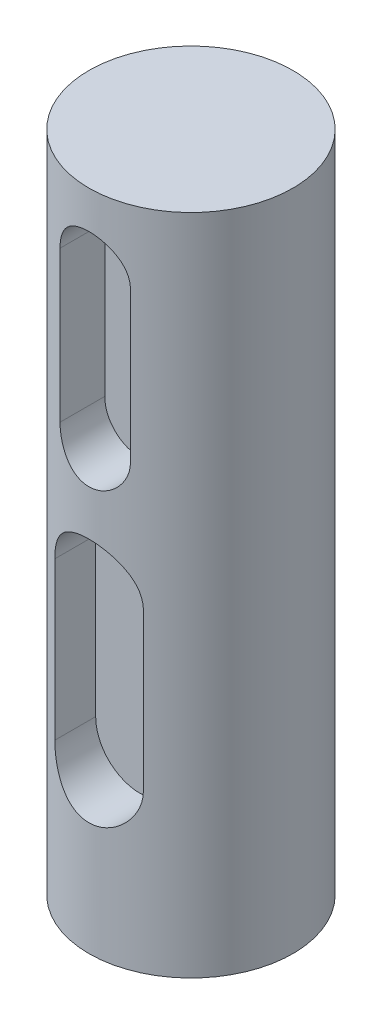
SolidWorks part; units mm, degrees
ref_plane "前视基准面" through (0, 0, 0) normal (0, 0, 1) x (1, 0, 0)
ref_plane "上视基准面" through (0, 0, 0) normal (0, 1, 0) x (1, 0, 0)
ref_plane "右视基准面" through (0, 0, 0) normal (1, 0, 0) x (0, 0, -1)
other "Configuration Table"
sketch "草图1" plane through (0, 0, 0) normal (0, 1, 0) x (1, 0, 0)
  circle A0 centre (0, 0) radius 10
  dimension "D1" = 20
ref_plane "基准面1" through (0, 10, 0) normal (0, 1, 0) x (1, 0, 0)
sketch "草图2" plane through (0, 10, 0) normal (0, 1, 0) x (1, 0, 0)
  circle A0 centre (0, 0) radius 10 construction
  circle A1 centre (0, 0) radius 10
extrude "凸台-拉伸1" add sketch "草图2" along normal blind 65
sketch "草图3" plane through (0, 0, 0) normal (0, 1, 0) x (1, 0, 0)
sketch "草图4" plane through (0, 0, 0) normal (0, 0, 1) x (1, 0, 0)
  line L0 (0, 40.8597) -> (0, 25.4566) construction
  line L1 (4.3418, 40.8597) -> (4.3418, 25.4566)
  line L2 (-4.3418, 40.8597) -> (-4.3418, 25.4566)
  arc A0 (4.3418, 40.8597) -> (-4.3418, 40.8597) centre (0, 40.8597) ccw
  arc A1 (-4.3418, 25.4566) -> (4.3418, 25.4566) centre (0, 25.4566) ccw
  point P3 (0, 33.1582)
ref_plane "基准面2" through (0, 0, 10) normal (0, 0, 1) x (1, 0, 0)
sketch "草图5" plane through (0, 0, 10) normal (0, 0, 1) x (1, 0, 0)
  line L0 (4.3418, 40.8597) -> (4.3418, 25.4566) construction
  line L1 (-4.3418, 40.8597) -> (-4.3418, 25.4566) construction
  line L2 (4.3418, 40.8597) -> (4.3418, 25.4566)
  line L3 (-4.3418, 40.8597) -> (-4.3418, 25.4566)
  arc A0 (4.3418, 40.8597) -> (-4.3418, 40.8597) centre (0, 40.8597) ccw construction
  arc A1 (-4.3418, 25.4566) -> (4.3418, 25.4566) centre (0, 25.4566) ccw construction
  arc A2 (4.3418, 40.8597) -> (-4.3418, 40.8597) centre (0, 40.8597) ccw
  arc A3 (-4.3418, 25.4566) -> (4.3418, 25.4566) centre (0, 25.4566) ccw
extrude "切除-拉伸2" cut sketch "草图5" against normal blind 5
sketch "草图6" plane through (0, 0, 10) normal (0, 0, 1) x (1, 0, 0)
  line L0 (0, 67.8686) -> (0, 53.0924) construction
  line L1 (3.4514, 67.8686) -> (3.4514, 53.0924)
  line L2 (-3.4514, 67.8686) -> (-3.4514, 53.0924)
  arc A0 (3.4514, 67.8686) -> (-3.4514, 67.8686) centre (0, 67.8686) ccw
  arc A1 (-3.4514, 53.0924) -> (3.4514, 53.0924) centre (0, 53.0924) ccw
  point P3 (0, 60.4805)
extrude "切除-拉伸3" cut sketch "草图6" against normal blind 5
